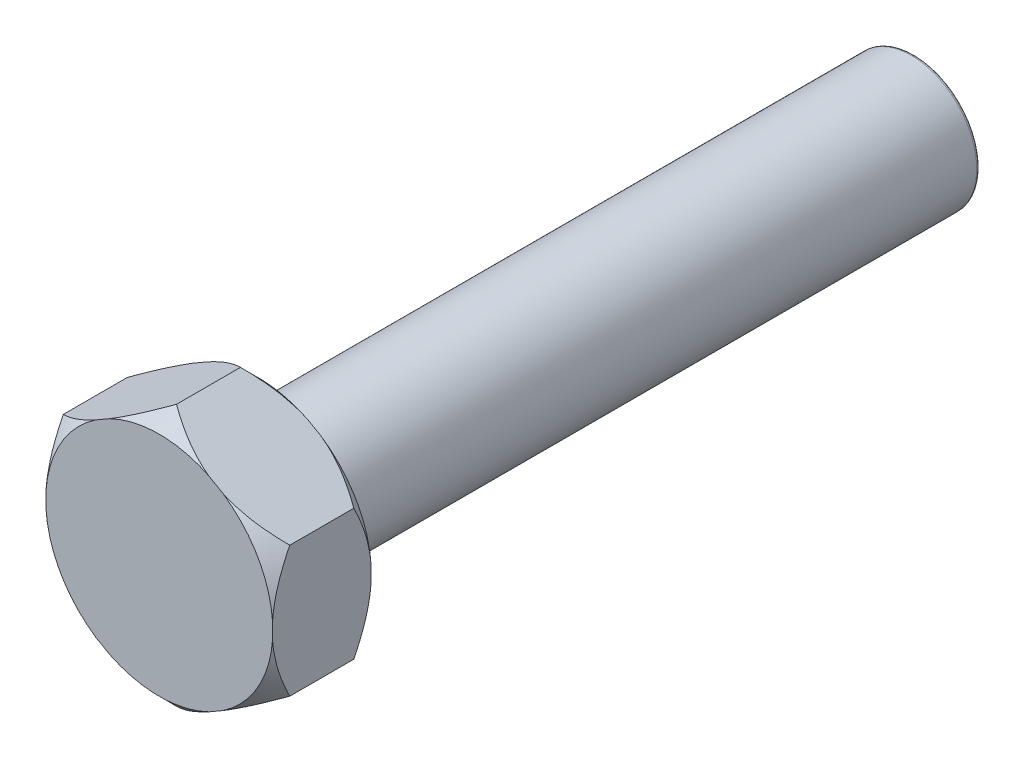
SolidWorks part; units mm, degrees
ref_plane "前视基准面" through (0, 0, 0) normal (0, 0, 1) x (1, 0, 0)
ref_plane "上视基准面" through (0, 0, 0) normal (0, 1, 0) x (1, 0, 0)
ref_plane "右视基准面" through (0, 0, 0) normal (1, 0, 0) x (0, 0, -1)
sketch "草图1" plane through (0, 0, 0) normal (0, 0, 1) x (1, 0, 0)
  line L1 (0, 7.9674) -> (-6.9, 3.9837)
  line L2 (-6.9, 3.9837) -> (-6.9, -3.9837)
  line L3 (-6.9, -3.9837) -> (0, -7.9674)
  line L4 (0, -7.9674) -> (6.9, -3.9837)
  line L5 (6.9, -3.9837) -> (6.9, 3.9837)
  line L6 (6.9, 3.9837) -> (0, 7.9674)
  circle A0 centre (0, 0) radius 6.9 construction
  dimension "D1" = 13.8
extrude "凸台-拉伸1" add sketch "草图1" against normal blind 6
sketch "草图2" plane through (0, 0, -6) normal (0, 0, -1) x (-1, 0, 0)
  circle A0 centre (0, 0) radius 4
extrude "凸台-拉伸2" add sketch "草图2" along normal blind 40
cosmetic thread "装饰螺纹线1" parameters "D1"=40, "D2"=6.619
sketch "草图3" plane through (0, 0, 0) normal (1, 0, 0) x (0, 0, -1)
  line L0 (0, 0) -> (-6.3071, 0) construction
  line L1 (0, -6.9174) -> (1.05, -7.9674)
  line L2 (0, -7.9674) -> (0, -3.9837) construction
  line L3 (6, -7.9674) -> (0, -7.9674) construction
  line L4 (1.05, -7.9674) -> (0, -7.9674)
  line L5 (0, -7.9674) -> (0, -6.9174)
  line L6 (6, -6.9174) -> (4.95, -7.9674)
  line L7 (6, -7.9674) -> (6, -3.9837) construction
  line L8 (4.95, -7.9674) -> (6, -7.9674)
  line L9 (6, -7.9674) -> (6, -6.9174)
revolve "切除-旋转1" cut sketch "草图3" angle 360 about L0
fillet "圆角3" radius 0.2 1 edges at (-4, 0, -46)
